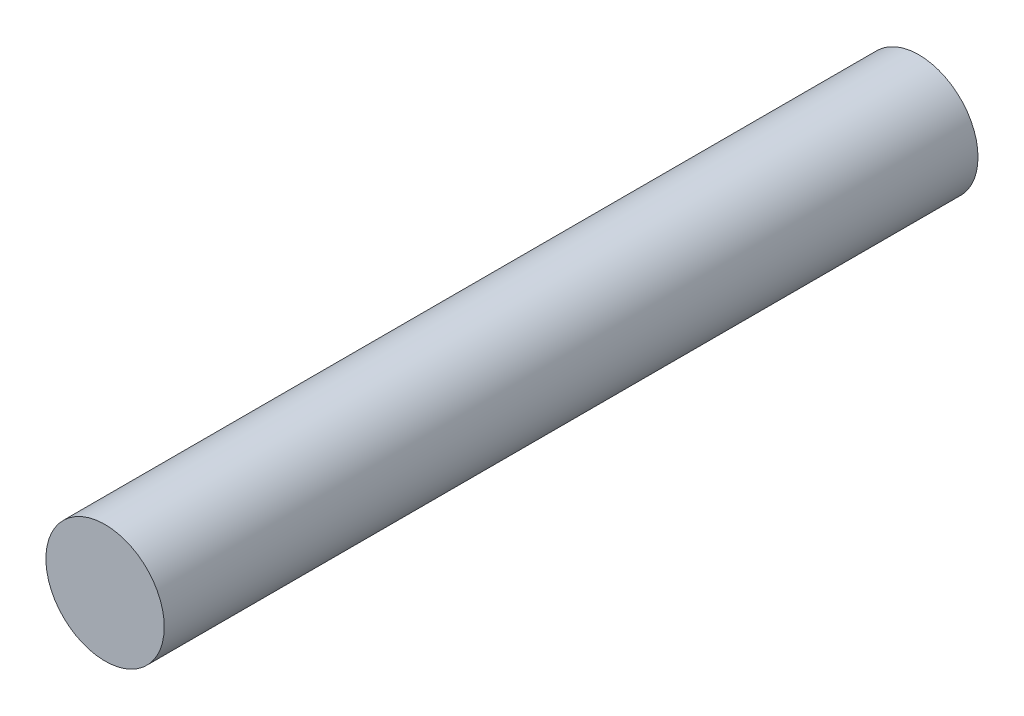
SolidWorks part; units mm, degrees
ref_plane "Front Plane" through (0, 0, 0) normal (0, 0, 1) x (1, 0, 0)
ref_plane "Top Plane" through (0, 0, 0) normal (0, 1, 0) x (1, 0, 0)
ref_plane "Right Plane" through (0, 0, 0) normal (1, 0, 0) x (0, 0, -1)
sketch "Sketch1" plane through (0, 0, 0) normal (0, 0, 1) x (1, 0, 0)
  circle A0 centre (0, 0) radius 2
  dimension "D1" = 4
extrude "Boss-Extrude1" add sketch "Sketch1" along normal blind 27.5
